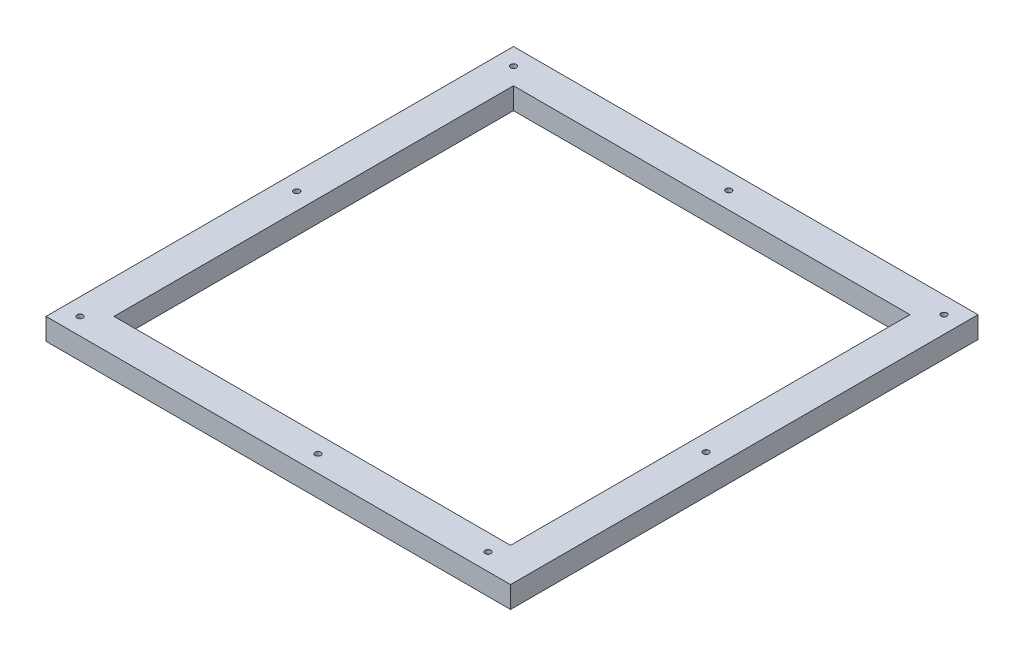
SolidWorks part; units mm, degrees
ref_plane "Front Plane" through (0, 0, 0) normal (0, 0, 1) x (1, 0, 0)
ref_plane "Top Plane" through (0, 0, 0) normal (0, 1, 0) x (1, 0, 0)
ref_plane "Right Plane" through (0, 0, 0) normal (1, 0, 0) x (0, 0, -1)
sketch "Sketch1" plane through (0, 0, 0) normal (0, 1, 0) x (1, 0, 0)
  line L1 (-136.635, 137.5) -> (136.635, 137.5)
  line L2 (-136.635, 137.5) -> (-136.635, -137.5)
  line L3 (-136.635, -137.5) -> (136.635, -137.5)
  line L4 (136.635, 137.5) -> (136.635, -137.5)
  line L5 (-136.635, 137.5) -> (136.635, -137.5) construction
  line L6 (-136.635, -137.5) -> (136.635, 137.5) construction
  point P0 (0, 0)
  dimension "D1" = 275
  dimension "D2" = 273.27
extrude "Boss-Extrude1" add sketch "Sketch1" along normal blind 12.7
sketch "Sketch2" plane through (0, 12.7, 0) normal (0, 1, 0) x (1, 0, 0)
  line L0 (136.635, 137.5) -> (-136.635, 137.5) construction
  line L1 (-116.635, 117.5) -> (116.635, 117.5)
  line L2 (-116.635, 117.5) -> (-116.635, -117.5)
  line L3 (-116.635, -117.5) -> (116.635, -117.5)
  line L4 (116.635, 117.5) -> (116.635, -117.5)
  line L5 (-116.635, 117.5) -> (116.635, -117.5) construction
  line L6 (-116.635, -117.5) -> (116.635, 117.5) construction
  line L7 (136.635, -137.5) -> (136.635, 137.5) construction
  point P0 (0, 0)
  dimension "D1" = 20
  dimension "D2" = 20
extrude "Cut-Extrude1" cut sketch "Sketch2" against normal blind 12.7
hole_wizard "M3 Clearance Hole1" positions "Sketch3" profile "Sketch4" hole size "M3" standard "ANSI Metric"
sketch "Sketch3" plane through (0, 12.7, 0) normal (0, 1, 0) x (1, 0, 0)
  point P0 (0, 127.5)
  point P3 (-126.635, 127.5)
  point P6 (126.6328, 127.5)
  point P9 (-126.635, 0)
  point P12 (-126.635, -128.0045)
  point P14 (13.3689, -127.5)
  point P17 (113.3689, -127.5)
  point P20 (126.6328, -12.5)
sketch "Sketch4" plane through (0, 12.7, -127.5) normal (1, 0, 0) x (0, 0, 1)
  line L0 (0, 0) -> (0, 12.7)
  line L1 (0, 12.7) -> (1.7, 12.7)
  line L2 (1.7, 12.7) -> (1.7, 0.025)
  line L3 (1.7, 0.025) -> (1.725, 0)
  line L5 (1.725, 0) -> (0, 0)
  line L6 (-1.7, 0.025) -> (-1.725, 0) construction
  line L11 (0, -6.35) -> (0, 107.95) construction
  dimension "Thru Hole Dia." = 3.4
  dimension "Thru Hole Depth" = 12.7
  dimension "Near C'Sink Dia." = 3.45
  dimension "Near C'Sink Angle" = 90
hole_wizard "M3 Clearance Hole2" positions "Sketch5" profile "Sketch6" hole size "M3" standard "ANSI Metric" end condition through all
sketch "Sketch5" plane through (0, 12.7, 0) normal (0, 1, 0) x (1, 0, 0)
  point P0 (-126.6311, -127.5)
sketch "Sketch6" plane through (-126.6311, 12.7, 127.5) normal (1, 0, 0) x (0, 0, 1)
  line L0 (0, 0) -> (0, 12.7)
  line L1 (0, 12.7) -> (1.7, 12.7)
  line L2 (1.7, 12.7) -> (1.7, 0.025)
  line L3 (1.7, 0.025) -> (1.725, 0)
  line L5 (1.725, 0) -> (0, 0)
  line L6 (-1.7, 0.025) -> (-1.725, 0) construction
  line L11 (0, -6.35) -> (0, 107.95) construction
  dimension "Thru Hole Dia." = 3.4
  dimension "Thru Hole Depth" = 12.7
  dimension "Near C'Sink Dia." = 3.45
  dimension "Near C'Sink Angle" = 90
